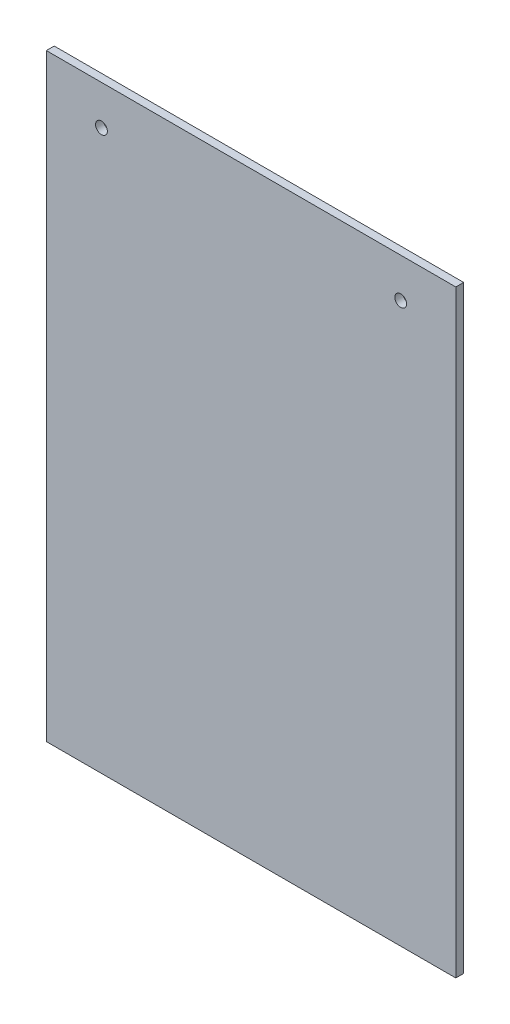
SolidWorks part; units mm, degrees
material "PC High Viscosity"
ref_plane "Front Plane" through (0, 0, 0) normal (0, 0, 1) x (1, 0, 0)
ref_plane "Top Plane" through (0, 0, 0) normal (0, 1, 0) x (1, 0, 0)
ref_plane "Right Plane" through (0, 0, 0) normal (1, 0, 0) x (0, 0, -1)
sketch "Sketch1" plane through (0, 0, 0) normal (0, 0, 1) x (1, 0, 0)
  line L1 (0, 0) -> (330.2, 0)
  line L2 (0, 0) -> (0, 482.6)
  line L3 (0, 482.6) -> (330.2, 482.6)
  line L4 (330.2, 0) -> (330.2, 482.6)
  dimension "D1" = 330.2
  dimension "D2" = 482.6
extrude "Boss-Extrude1" add sketch "Sketch1" along normal blind 6.35
hole_wizard "3/8 (0.375) Diameter Hole1" positions "Sketch2" profile "Sketch3" hole size "3/8" standard "ANSI Inch" end condition through all
sketch "Sketch2" plane through (0, 0, 6.35) normal (0, 0, 1) x (1, 0, 0)
  line L0 (165.1, 482.6) -> (165.1, 0) construction
  line L1 (330.2, 482.6) -> (0, 482.6) construction
  line L2 (0, 0) -> (330.2, 0) construction
  line L4 (0, 482.6) -> (0, 0) construction
  point P0 (44.45, 450.85)
  point P2 (285.75, 450.85)
  dimension "D1" = 44.45
  dimension "D2" = 450.85
sketch "Sketch3" plane through (44.45, 450.85, 6.35) normal (1, 0, 0) x (0, -1, 0)
  line L0 (0, 0) -> (0, 6.35)
  line L1 (0, 6.35) -> (4.7625, 6.35)
  line L2 (4.7625, 6.35) -> (4.7625, 0)
  line L5 (4.7625, 0) -> (0, 0)
  line L11 (0, -6.35) -> (0, 107.95) construction
  dimension "Thru Hole Dia." = 9.525
  dimension "Thru Hole Depth" = 6.35
